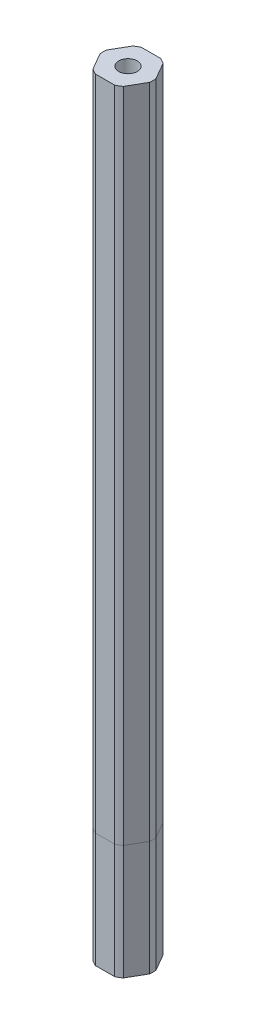
SolidWorks part; units mm, degrees
material "1060 Alloy"
ref_plane "Front Plane" through (0, 0, 0) normal (0, 0, 1) x (1, 0, 0)
ref_plane "Top Plane" through (0, 0, 0) normal (0, 1, 0) x (1, 0, 0)
ref_plane "Right Plane" through (0, 0, 0) normal (1, 0, 0) x (0, 0, -1)
sketch "Sketch1" plane through (0, 0, 0) normal (0, 1, 0) x (1, 0, 0)
  line L1 (6.8178, 0.8913) -> (4.1808, 5.4587)
  line L2 (2.637, 6.35) -> (-2.637, 6.35)
  line L3 (-4.1808, 5.4587) -> (-6.8178, 0.8913)
  line L4 (-6.8178, -0.8913) -> (-4.1808, -5.4587)
  line L5 (-2.637, -6.35) -> (2.637, -6.35)
  line L6 (4.1808, -5.4587) -> (6.8178, -0.8913)
  circle A0 centre (0, 0) radius 6.35 construction
  arc A1 (-2.637, 6.35) -> (-4.1808, 5.4587) centre (0, 0) ccw
  arc A3 (4.1808, 5.4587) -> (2.637, 6.35) centre (0, 0) ccw
  arc A4 (6.8178, -0.8913) -> (6.8178, 0.8913) centre (0, 0) ccw
  arc A5 (-6.8178, 0.8913) -> (-6.8178, -0.8913) centre (0, 0) ccw
  arc A6 (-4.1808, -5.4587) -> (-2.637, -6.35) centre (0, 0) ccw
  arc A7 (2.637, -6.35) -> (4.1808, -5.4587) centre (0, 0) ccw
  circle A8 centre (0, 0) radius 4.0005
  dimension "D2" = 13.7516
  dimension "D3" = 8.001
  dimension "D1" = 12.7
  dimension "D4" = 4.5674
extrude "Boss-Extrude1" add sketch "Sketch1" along normal blind 31.623
sketch "Sketch2" plane through (0, 31.623, 0) normal (0, 1, 0) x (1, 0, 0)
  line L6 (2.637, 6.35) -> (-2.637, 6.35)
  line L7 (-4.1808, 5.4587) -> (-6.8178, 0.8913)
  line L8 (-6.8178, -0.8913) -> (-4.1808, -5.4587)
  line L9 (-2.637, -6.35) -> (2.637, -6.35)
  line L10 (4.1808, -5.4587) -> (6.8178, -0.8913)
  line L11 (6.8178, 0.8913) -> (4.1808, 5.4587)
  line L12 (2.637, 6.35) -> (-2.637, 6.35)
  line L13 (-4.1808, 5.4587) -> (-6.8178, 0.8913)
  line L14 (-6.8178, -0.8913) -> (-4.1808, -5.4587)
  line L15 (-2.637, -6.35) -> (2.637, -6.35)
  line L16 (4.1808, -5.4587) -> (6.8178, -0.8913)
  line L17 (6.8178, 0.8913) -> (4.1808, 5.4587)
  circle A0 centre (0, 0) radius 2.5527
  arc A9 (4.1808, 5.4587) -> (2.637, 6.35) centre (0, 0) ccw
  arc A10 (-2.637, 6.35) -> (-4.1808, 5.4587) centre (0, 0) ccw
  arc A11 (-6.8178, 0.8913) -> (-6.8178, -0.8913) centre (0, 0) ccw
  arc A12 (-4.1808, -5.4587) -> (-2.637, -6.35) centre (0, 0) ccw
  arc A13 (2.637, -6.35) -> (4.1808, -5.4587) centre (0, 0) ccw
  arc A14 (6.8178, -0.8913) -> (6.8178, 0.8913) centre (0, 0) ccw
  arc A15 (4.1808, 5.4587) -> (2.637, 6.35) centre (0, 0) ccw
  arc A16 (-2.637, 6.35) -> (-4.1808, 5.4587) centre (0, 0) ccw
  arc A17 (-6.8178, 0.8913) -> (-6.8178, -0.8913) centre (0, 0) ccw
  arc A18 (-4.1808, -5.4587) -> (-2.637, -6.35) centre (0, 0) ccw
  arc A19 (2.637, -6.35) -> (4.1808, -5.4587) centre (0, 0) ccw
  arc A20 (6.8178, -0.8913) -> (6.8178, 0.8913) centre (0, 0) ccw
  dimension "D1" = 5.1054
  dimension "D3" = 0
extrude "Boss-Extrude2" add sketch "Sketch2" along normal blind 181.102 separate body
